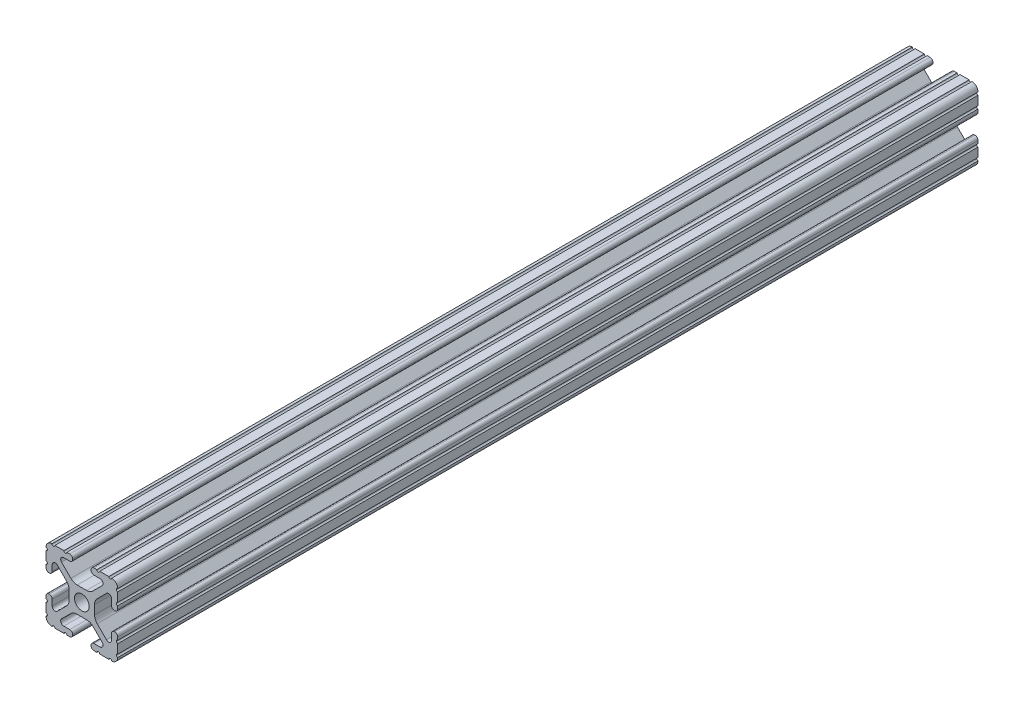
SolidWorks part; units mm, degrees
material "6061 Alloy"
ref_plane "Front Plane" through (0, 0, 0) normal (0, 0, 1) x (1, 0, 0)
ref_plane "Top Plane" through (0, 0, 0) normal (0, 1, 0) x (1, 0, 0)
ref_plane "Right Plane" through (0, 0, 0) normal (1, 0, 0) x (0, 0, -1)
sketch "Sketch1" plane through (0, 0, 0) normal (0, 0, 1) x (1, 0, 0)
  line L0 (-7.2072, 8.7245) -> (-3.9003, 5.4237)
  line L1 (-4.2875, 10.4902) -> (-6.4768, 10.4902)
  line L2 (-3.2384, 11.651) -> (-3.2384, 11.5392)
  line L3 (-5.3171, 12.7) -> (-4.2875, 12.7)
  line L4 (0, 13.4005) -> (0, -14.8534) construction
  line L5 (12.7, 0) -> (-13.9989, 0) construction
  line L6 (-9.5504, 12.7) -> (-6.3331, 12.7)
  line L7 (-12.7, 6.3331) -> (-12.7, 9.5504)
  line L8 (-12.7, 4.2875) -> (-12.7, 5.3171)
  line L9 (-11.5392, 3.2385) -> (-11.651, 3.2385)
  line L10 (-10.4902, 6.4021) -> (-10.4902, 4.2875)
  line L11 (-5.4405, 3.8388) -> (-8.737, 7.1292)
  line L12 (-4.5085, -1.5917) -> (-4.5085, 1.5917)
  line L13 (-1.7093, -4.4958) -> (1.7093, -4.4958)
  line L14 (3.9523, -5.4237) -> (7.1797, -8.6452)
  line L15 (6.4164, -10.4902) -> (4.2875, -10.4902)
  line L16 (3.2385, -11.5392) -> (3.2385, -11.651)
  line L17 (4.2875, -12.7) -> (5.3171, -12.7)
  line L18 (6.3331, -12.7) -> (9.5504, -12.7)
  line L19 (12.7, -9.5504) -> (12.7, -6.3331)
  line L20 (12.7, -5.3171) -> (12.7, -4.2875)
  line L21 (11.651, -3.2385) -> (11.5392, -3.2385)
  line L22 (10.4902, -4.2875) -> (10.4902, -6.4021)
  line L23 (8.737, -7.1292) -> (5.4405, -3.8388)
  line L24 (4.5085, -1.5917) -> (4.5085, 1.5917)
  line L25 (5.4405, 3.8388) -> (8.737, 7.1292)
  line L26 (10.4902, 6.4021) -> (10.4902, 4.2875)
  line L27 (11.5392, 3.2385) -> (11.651, 3.2385)
  line L28 (12.7, 4.2875) -> (12.7, 5.3171)
  line L29 (12.7, 6.3331) -> (12.7, 9.5504)
  line L30 (9.5504, 12.7) -> (6.3331, 12.7)
  line L31 (5.3171, 12.7) -> (4.2875, 12.7)
  line L32 (3.2384, 11.651) -> (3.2384, 11.5392)
  line L33 (4.2875, 10.4902) -> (6.4768, 10.4902)
  line L34 (7.2072, 8.7245) -> (3.9003, 5.4237)
  line L35 (1.6573, 4.4958) -> (-1.6573, 4.4958)
  line L36 (-8.737, -7.1292) -> (-5.4405, -3.8388)
  line L37 (-10.4902, -4.2875) -> (-10.4902, -6.4021)
  line L38 (-11.651, -3.2385) -> (-11.5392, -3.2385)
  line L39 (-12.7, -5.3171) -> (-12.7, -4.2875)
  line L40 (-12.7, -9.5504) -> (-12.7, -6.3331)
  line L41 (-6.3331, -12.7) -> (-9.5504, -12.7)
  line L42 (-4.2875, -12.7) -> (-5.3171, -12.7)
  line L43 (-3.2385, -11.5392) -> (-3.2385, -11.651)
  line L44 (-6.4164, -10.4902) -> (-4.2875, -10.4902)
  line L45 (-3.9523, -5.4237) -> (-7.1797, -8.6452)
  arc A0 (-7.2072, 8.7245) -> (-6.4768, 10.4902) centre (-6.4768, 9.4563) cw
  arc A1 (-3.2384, 11.5392) -> (-4.2875, 10.4902) centre (-4.2875, 11.5392) cw
  arc A2 (-4.2875, 12.7) -> (-3.2384, 11.651) centre (-4.2875, 11.651) cw
  arc A3 (-5.3171, 12.7) -> (-6.3331, 12.7) centre (-5.8251, 12.7) cw
  arc A4 (-9.5504, 12.7) -> (-10.5664, 12.6998) centre (-10.0584, 12.7) cw
  arc A5 (-12.6998, 10.5664) -> (-10.5664, 12.6998) centre (-10.5918, 10.5918) cw
  arc A6 (-12.6998, 10.5664) -> (-12.7, 9.5504) centre (-12.7, 10.0584) cw
  arc A7 (-12.7, 6.3331) -> (-12.7, 5.3171) centre (-12.7, 5.8251) cw
  arc A8 (-11.651, 3.2385) -> (-12.7, 4.2875) centre (-11.651, 4.2875) cw
  arc A9 (-10.4902, 4.2875) -> (-11.5392, 3.2385) centre (-11.5392, 4.2875) cw
  circle A10 centre (0, 0) radius 2.6035
  arc A11 (-10.4902, 6.4021) -> (-8.737, 7.1292) centre (-9.4628, 6.4021) cw
  arc A12 (-5.4405, 3.8388) -> (-4.5085, 1.5917) centre (-7.6835, 1.5917) cw
  arc A13 (-4.5085, -1.5917) -> (-5.4405, -3.8388) centre (-7.6835, -1.5917) cw
  arc A14 (-8.737, -7.1292) -> (-10.4902, -6.4021) centre (-9.4628, -6.4021) cw
  arc A15 (-1.7093, -4.4958) -> (-3.9523, -5.4237) centre (-1.7093, -7.6708) ccw
  arc A16 (3.9523, -5.4237) -> (1.7093, -4.4958) centre (1.7093, -7.6708) ccw
  arc A17 (6.4164, -10.4902) -> (7.1797, -8.6452) centre (6.4164, -9.4098) ccw
  arc A18 (4.2875, -10.4902) -> (3.2385, -11.5392) centre (4.2875, -11.5392) ccw
  arc A19 (3.2385, -11.651) -> (4.2875, -12.7) centre (4.2875, -11.651) ccw
  arc A20 (6.3331, -12.7) -> (5.3171, -12.7) centre (5.8251, -12.7) ccw
  arc A21 (10.5664, -12.6998) -> (9.5504, -12.7) centre (10.0584, -12.7) ccw
  arc A22 (10.5664, -12.6998) -> (12.6998, -10.5664) centre (10.5918, -10.5918) ccw
  arc A23 (12.7, -9.5504) -> (12.6998, -10.5664) centre (12.7, -10.0584) ccw
  arc A24 (12.7, -5.3171) -> (12.7, -6.3331) centre (12.7, -5.8251) ccw
  arc A25 (12.7, -4.2875) -> (11.651, -3.2385) centre (11.651, -4.2875) ccw
  arc A26 (11.5392, -3.2385) -> (10.4902, -4.2875) centre (11.5392, -4.2875) ccw
  arc A27 (8.737, -7.1292) -> (10.4902, -6.4021) centre (9.4628, -6.4021) ccw
  arc A28 (4.5085, -1.5917) -> (5.4405, -3.8388) centre (7.6835, -1.5917) ccw
  arc A29 (5.4405, 3.8388) -> (4.5085, 1.5917) centre (7.6835, 1.5917) ccw
  arc A30 (10.4902, 6.4021) -> (8.737, 7.1292) centre (9.4628, 6.4021) ccw
  arc A31 (10.4902, 4.2875) -> (11.5392, 3.2385) centre (11.5392, 4.2875) ccw
  arc A32 (11.651, 3.2385) -> (12.7, 4.2875) centre (11.651, 4.2875) ccw
  arc A33 (12.7, 6.3331) -> (12.7, 5.3171) centre (12.7, 5.8251) ccw
  arc A34 (12.6998, 10.5664) -> (12.7, 9.5504) centre (12.7, 10.0584) ccw
  arc A35 (12.6998, 10.5664) -> (10.5664, 12.6998) centre (10.5918, 10.5918) ccw
  arc A36 (9.5504, 12.7) -> (10.5664, 12.6998) centre (10.0584, 12.7) ccw
  arc A37 (5.3171, 12.7) -> (6.3331, 12.7) centre (5.8251, 12.7) ccw
  arc A38 (4.2875, 12.7) -> (3.2384, 11.651) centre (4.2875, 11.651) ccw
  arc A39 (3.2384, 11.5392) -> (4.2875, 10.4902) centre (4.2875, 11.5392) ccw
  arc A40 (7.2072, 8.7245) -> (6.4768, 10.4902) centre (6.4768, 9.4563) ccw
  arc A41 (1.6573, 4.4958) -> (3.9003, 5.4237) centre (1.6573, 7.6708) ccw
  arc A42 (-1.6573, 4.4958) -> (-3.9003, 5.4237) centre (-1.6573, 7.6708) cw
  arc A43 (-11.5392, -3.2385) -> (-10.4902, -4.2875) centre (-11.5392, -4.2875) cw
  arc A44 (-12.7, -4.2875) -> (-11.651, -3.2385) centre (-11.651, -4.2875) cw
  arc A45 (-12.7, -5.3171) -> (-12.7, -6.3331) centre (-12.7, -5.8251) cw
  arc A46 (-12.7, -9.5504) -> (-12.6998, -10.5664) centre (-12.7, -10.0584) cw
  arc A47 (-10.5664, -12.6998) -> (-12.6998, -10.5664) centre (-10.5918, -10.5918) cw
  arc A48 (-10.5664, -12.6998) -> (-9.5504, -12.7) centre (-10.0584, -12.7) cw
  arc A49 (-6.3331, -12.7) -> (-5.3171, -12.7) centre (-5.8251, -12.7) cw
  arc A50 (-3.2385, -11.651) -> (-4.2875, -12.7) centre (-4.2875, -11.651) cw
  arc A51 (-4.2875, -10.4902) -> (-3.2385, -11.5392) centre (-4.2875, -11.5392) cw
  arc A52 (-6.4164, -10.4902) -> (-7.1797, -8.6452) centre (-6.4164, -9.4098) cw
  dimension "D1" = 5.207
  dimension "D9" = 14.859
  dimension "D2" = 25.4
  dimension "D3" = 12.7
  dimension "D4" = 6.477
  dimension "D5" = 8.2042
  dimension "D6" = 9.017
  dimension "D8" = 2.2098
  dimension "D10" = 2.2098
extrude "Extrude1" add sketch "Sketch1" against normal blind 304.8
